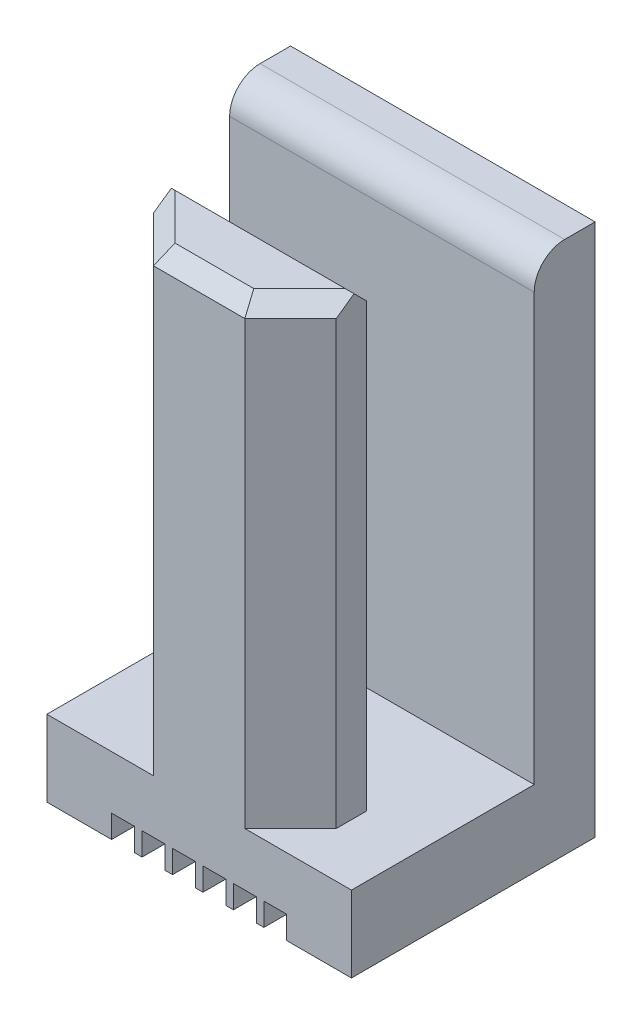
SolidWorks part; units mm, degrees
ref_plane "前视基准面" through (0, 0, 0) normal (0, 0, 1) x (1, 0, 0)
ref_plane "上视基准面" through (0, 0, 0) normal (0, 1, 0) x (1, 0, 0)
ref_plane "右视基准面" through (0, 0, 0) normal (1, 0, 0) x (0, 0, -1)
sketch "草图1" plane through (0, 0, 0) normal (0, 1, 0) x (1, 0, 0)
  line L1 (-11.8673, 6.4735) -> (8.1327, 6.4735)
  line L2 (-11.8673, 6.4735) -> (-11.8673, -9.5265)
  line L3 (-11.8673, -9.5265) -> (8.1327, -9.5265)
  line L4 (8.1327, 6.4735) -> (8.1327, -9.5265)
  dimension "D1" = 16
  dimension "D2" = 20
extrude "凸台-拉伸1" add sketch "草图1" along normal blind 5
sketch "草图2" plane through (0, 5, 0) normal (0, 1, 0) x (1, 0, 0)
  line L0 (-1.8673, -9.5265) -> (1.1327, -9.5265)
  line L1 (-11.8673, -9.5265) -> (8.1327, -9.5265) construction
  line L2 (-1.8673, -9.5265) -> (-1.8673, -4.5265) construction
  line L3 (-1.8673, -4.5265) -> (6.1327, -4.5265)
  line L4 (6.1327, -4.5265) -> (1.1327, -9.5265)
  line L5 (-1.8673, -4.5265) -> (-9.8673, -4.5265)
  line L6 (-9.8673, -4.5265) -> (-4.8673, -9.5265)
  line L7 (-4.8673, -9.5265) -> (-1.8673, -9.5265)
  line L8 (8.1327, -9.5265) -> (8.1327, 6.4735) construction
  line L9 (-11.8673, 6.4735) -> (8.1327, 6.4735)
  line L10 (-11.8673, 6.4735) -> (-11.8673, 2.4735)
  line L11 (-11.8673, 2.4735) -> (8.1327, 2.4735)
  line L12 (8.1327, 6.4735) -> (8.1327, 2.4735)
  dimension "D1" = 4
extrude "凸台-拉伸2" add sketch "草图2" along normal blind 30
chamfer "倒角1" distance 1 angle 45 4 edges at (-7.3673, 35, 7.0265) (-1.8673, 35, 4.5265) (3.6327, 35, 7.0265) (-1.8673, 35, 9.5265)
fillet "圆角1" radius 2 1 edges at (-1.8673, 35, -2.4735)
sketch "草图3" plane through (0, 0, -6.4735) normal (0, 0, -1) x (-1, 0, 0)
  line L0 (1.8673, 0) -> (2.8673, 0) construction
  line L1 (-8.1327, 0) -> (11.8673, 0) construction
  line L2 (2.8673, 0) -> (4.8673, 0) construction
  line L3 (4.8673, 0) -> (6.8673, 0) construction
  line L4 (1.8673, 0) -> (0.8673, 0) construction
  line L5 (0.8673, 0) -> (-1.1327, 0) construction
  line L6 (-1.1327, 0) -> (-3.1327, 0) construction
  line L8 (-3.8827, 0) -> (-2.3827, 0)
  line L9 (-3.8827, 0) -> (-3.8827, 1.5)
  line L10 (-3.8827, 1.5) -> (-2.3827, 1.5)
  line L11 (-2.3827, 0) -> (-2.3827, 1.5)
  line L12 (-1.8827, 0) -> (-0.3827, 0)
  line L13 (-1.8827, 0) -> (-1.8827, 1.5)
  line L14 (-1.8827, 1.5) -> (-0.3827, 1.5)
  line L15 (-0.3827, 0) -> (-0.3827, 1.5)
  line L16 (0.1173, 0) -> (1.6173, 0)
  line L17 (0.1173, 0) -> (0.1173, 1.5)
  line L18 (0.1173, 1.5) -> (1.6173, 1.5)
  line L19 (1.6173, 0) -> (1.6173, 1.5)
  line L20 (2.1173, 0) -> (3.6173, 0)
  line L21 (2.1173, 0) -> (2.1173, 1.5)
  line L22 (2.1173, 1.5) -> (3.6173, 1.5)
  line L23 (3.6173, 0) -> (3.6173, 1.5)
  line L24 (4.1173, 0) -> (5.6173, 0)
  line L25 (4.1173, 0) -> (4.1173, 1.5)
  line L26 (4.1173, 1.5) -> (5.6173, 1.5)
  line L27 (5.6173, 0) -> (5.6173, 1.5)
  line L28 (6.1173, 0) -> (7.6173, 0)
  line L29 (6.1173, 0) -> (6.1173, 1.5)
  line L30 (6.1173, 1.5) -> (7.6173, 1.5)
  line L31 (7.6173, 0) -> (7.6173, 1.5)
  dimension "D7" = 1.5
  dimension "D1" = 1
  dimension "D2" = 2
  dimension "D3" = 2
  dimension "D4" = 1
  dimension "D5" = 2
  dimension "D6" = 2
  dimension "D8" = 1.5
  dimension "D9" = 1.5
  dimension "D10" = 1.5
  dimension "D11" = 1.5
  dimension "D12" = 1.5
extrude "切除-拉伸1" cut sketch "草图3" against normal through all
sketch "草图5" plane through (0, 5, 0) normal (0, 1, 0) x (1, 0, 0)
  line L1 (-9.8673, -4.5265) -> (-7.8673, -4.5265)
  line L2 (-9.8673, -4.5265) -> (-9.8673, -7.5246)
  line L3 (-9.8673, -7.5246) -> (-7.8673, -7.5246)
  line L4 (-7.8673, -4.5265) -> (-7.8673, -7.5246)
  line L5 (6.1327, -4.5265) -> (4.1327, -4.5265)
  line L6 (6.1327, -4.5265) -> (6.1327, -7.6288)
  line L7 (6.1327, -7.6288) -> (4.1327, -7.6288)
  line L8 (4.1327, -4.5265) -> (4.1327, -7.6288)
  dimension "D1" = 2
  dimension "D2" = 2
extrude "切除-拉伸2" cut sketch "草图5" along normal through all
